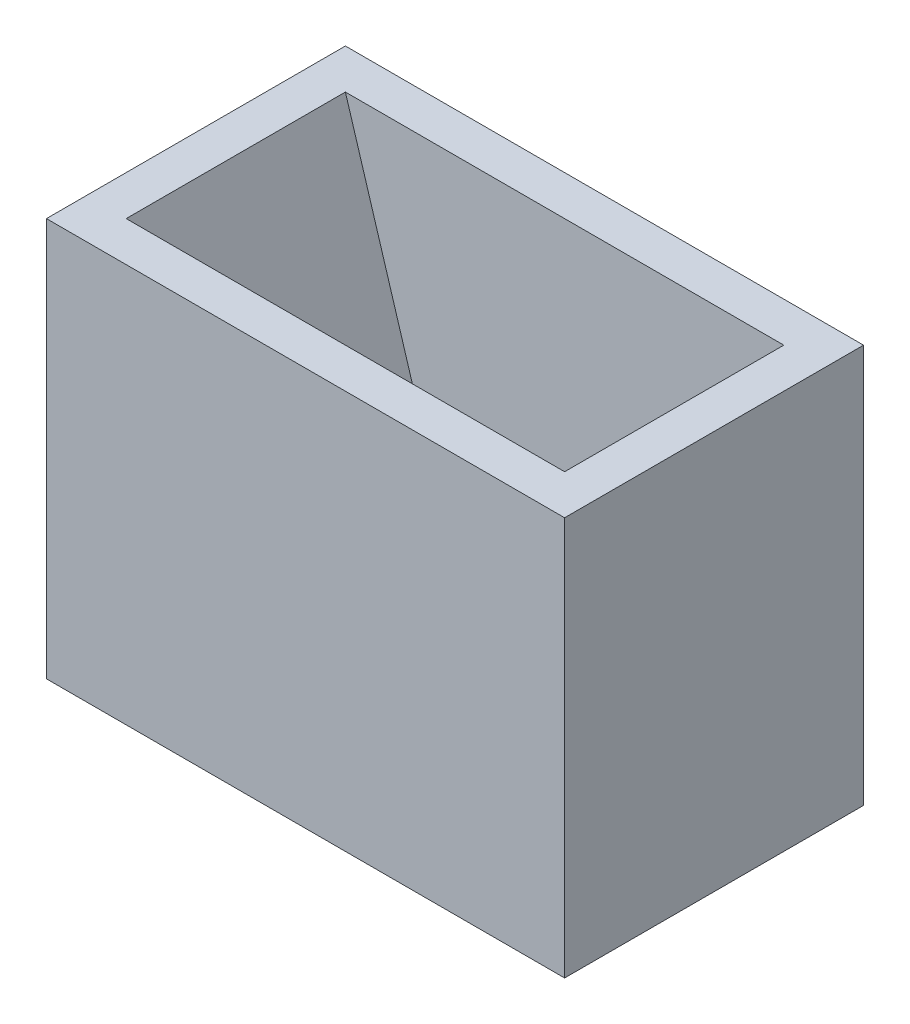
SolidWorks part; units mm, degrees
ref_plane "Front Plane" through (0, 0, 0) normal (0, 0, 1) x (1, 0, 0)
ref_plane "Top Plane" through (0, 0, 0) normal (0, 1, 0) x (1, 0, 0)
ref_plane "Right Plane" through (0, 0, 0) normal (1, 0, 0) x (0, 0, -1)
sketch "Sketch1" plane through (0, 0, 0) normal (0, 1, 0) x (1, 0, 0)
  line L0 (-6.5, 3.75) -> (6.5, 3.75)
  line L1 (-5.5, 2.75) -> (5.5, 2.75)
  line L2 (-5.5, 2.75) -> (-5.5, -2.75)
  line L3 (-5.5, -2.75) -> (5.5, -2.75)
  line L4 (5.5, 2.75) -> (5.5, -2.75)
  line L5 (-5.5, 2.75) -> (5.5, -2.75) construction
  line L6 (-5.5, -2.75) -> (5.5, 2.75) construction
  line L7 (6.5, 3.75) -> (6.5, -3.75)
  line L8 (-6.5, -3.75) -> (6.5, -3.75)
  line L9 (-6.5, 3.75) -> (-6.5, -3.75)
  point P0 (0, 0)
  dimension "D1" = 5.5
  dimension "D2" = 11
  dimension "D3" = 1
extrude "Boss-Extrude1" add sketch "Sketch1" along normal blind 10
sketch "Sketch2" plane through (0, 0, 0) normal (0, -1, 0) x (1, 0, 0)
  line L1 (-6.5, 3.75) -> (6.5, 3.75)
  line L2 (-6.5, 3.75) -> (-6.5, -3.75)
  line L3 (-6.5, -3.75) -> (6.5, -3.75)
  line L4 (6.5, 3.75) -> (6.5, -3.75)
  line L5 (-6.5, 3.75) -> (6.5, -3.75) construction
  line L6 (-6.5, -3.75) -> (6.5, 3.75) construction
  circle A0 centre (0, 0) radius 2.75
  point P0 (0, 0)
  dimension "D1" = 5.5
extrude "Boss-Extrude2" add sketch "Sketch2" against normal blind 1
sketch "Sketch4" plane through (0, 0, 0) normal (0, 0, 1) x (1, 0, 0)
  line L0 (-5.5, 10) -> (-2.75, 1)
  line L1 (-5.5, 1) -> (0, 1) construction
  line L2 (-2.75, 1) -> (-5.5, 1)
  line L3 (-5.5, 1) -> (-5.5, 10)
  line L4 (5.5, 10) -> (2.75, 1)
  line L6 (2.75, 1) -> (5.5, 1)
  line L7 (5.5, 1) -> (5.5, 10)
  point P12 (1.1833, 1)
extrude "Boss-Extrude3" add sketch "Sketch4" along normal mid plane 6
